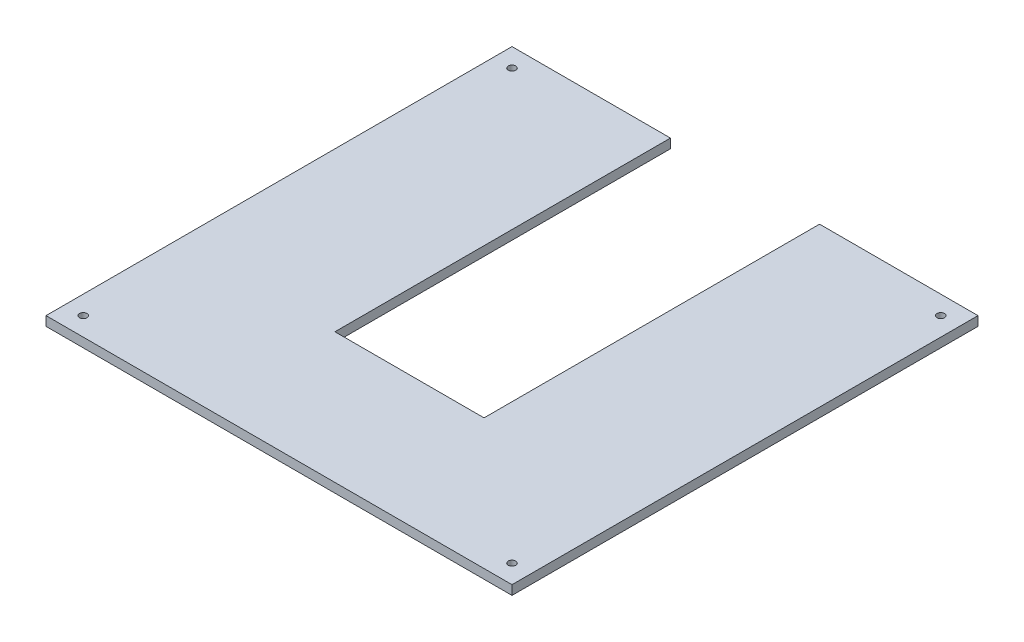
SolidWorks part; units mm, degrees
material "Pinho"
ref_plane "Plano frontal" through (0, 0, 0) normal (0, 0, 1) x (1, 0, 0)
ref_plane "Plano superior" through (0, 0, 0) normal (0, 1, 0) x (1, 0, 0)
ref_plane "Plano direito" through (0, 0, 0) normal (1, 0, 0) x (0, 0, -1)
sketch "Esboço1" plane through (0, 0, 0) normal (0, 1, 0) x (1, 0, 0)
  line L0 (0, 125) -> (0, -55) construction
  line L1 (-125, 125) -> (-40, 125)
  line L2 (-125, 125) -> (-125, -125)
  line L3 (-125, -125) -> (125, -125)
  line L4 (125, 125) -> (125, -125)
  line L5 (-125, 125) -> (125, -125) construction
  line L6 (-125, -125) -> (125, 125) construction
  line L7 (-40, 125) -> (-40, -55)
  line L8 (40, 125) -> (40, -55)
  line L9 (-125, 115) -> (-115, 115) construction
  line L10 (-40, -55) -> (40, -55)
  line L11 (40, 125) -> (125, 125)
  line L12 (-125, 0) -> (125, 0) construction
  circle A0 centre (-115, 115) radius 2
  circle A1 centre (115, 115) radius 2
  circle A2 centre (-115, -115) radius 2
  circle A3 centre (115, -115) radius 2
  point P0 (0, 0)
  dimension "D1" = 250
  dimension "D2" = 250
  dimension "D3" = 40
  dimension "D4" = 40
extrude "Ressalto-extrusão1" add sketch "Esboço1" along normal blind 5
